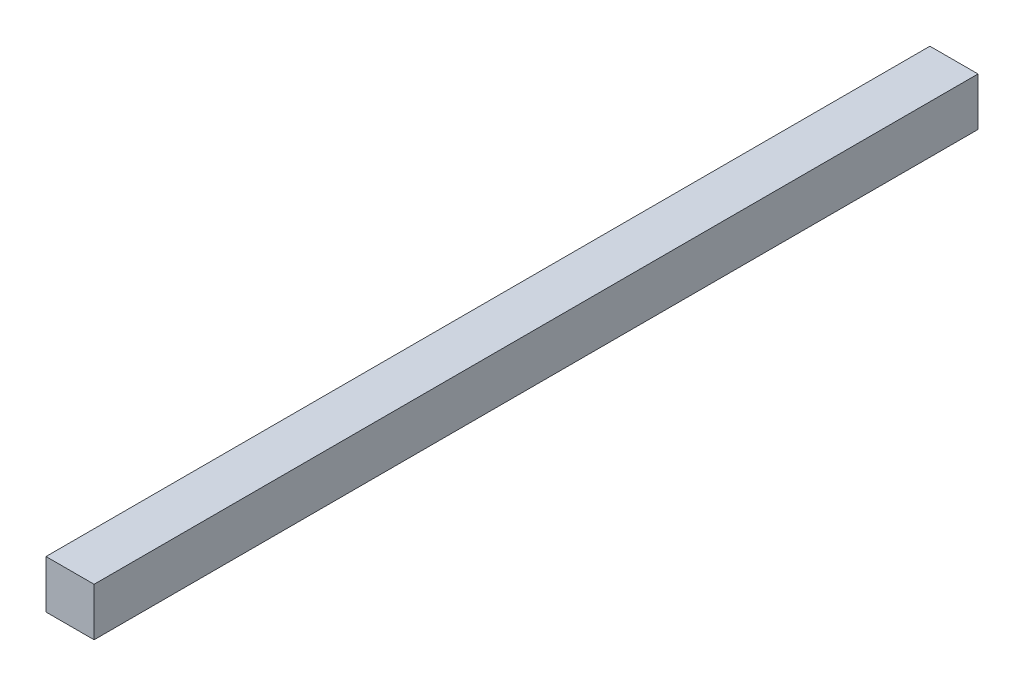
SolidWorks part; units mm, degrees
material "Balsa"
ref_plane "Front Plane" through (0, 0, 0) normal (0, 0, 1) x (1, 0, 0)
ref_plane "Top Plane" through (0, 0, 0) normal (0, 1, 0) x (1, 0, 0)
ref_plane "Right Plane" through (0, 0, 0) normal (1, 0, 0) x (0, 0, -1)
sketch "Sketch1" plane through (0, 0, 0) normal (0, 0, 1) x (1, 0, 0)
  line L1 (0, 0) -> (3.175, 0)
  line L2 (0, 0) -> (0, 3.175)
  line L3 (0, 3.175) -> (3.175, 3.175)
  line L4 (3.175, 0) -> (3.175, 3.175)
  dimension "D1" = 3.175
extrude "Boss-Extrude1" add sketch "Sketch1" along normal blind 58.35
